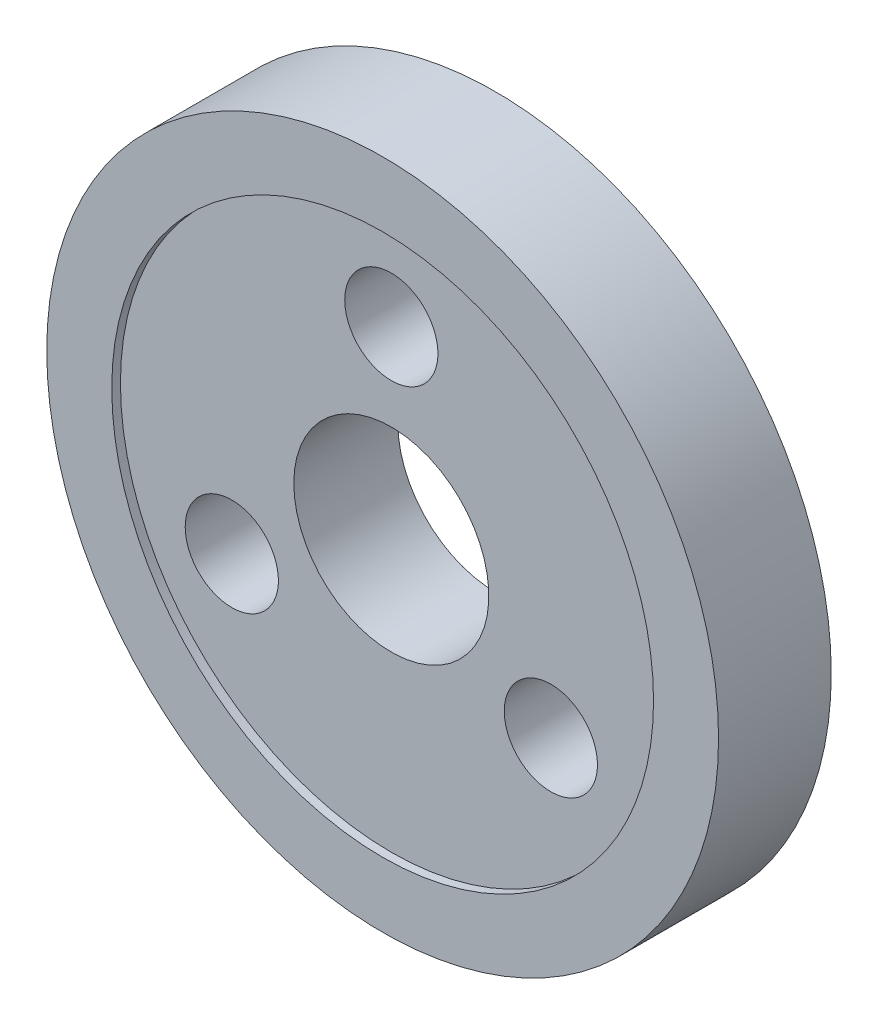
SolidWorks part; units mm, degrees
material "PE Low/Medium Density"
ref_plane "Front Plane" through (0, 0, 0) normal (0, 0, 1) x (1, 0, 0)
ref_plane "Top Plane" through (0, 0, 0) normal (0, 1, 0) x (1, 0, 0)
ref_plane "Right Plane" through (0, 0, 0) normal (1, 0, 0) x (0, 0, -1)
sketch "Sketch1" plane through (0, 0, 0) normal (0, 0, 1) x (1, 0, 0)
  circle A0 centre (0, 0) radius 12.5
  circle A1 centre (0, 0) radius 15.5
  dimension "D1" = 25
  dimension "D2" = 3
extrude "Boss-Extrude1" add sketch "Sketch1" along normal blind 0.4
sketch "Sketch2" plane through (0, 0, 0) normal (0, 0, -1) x (-1, 0, 0)
  circle A0 centre (0, 0) radius 15.5
  circle A1 centre (0, 0) radius 4.5
  circle A3 centre (0, 0) radius 15.5 construction
  dimension "D2" = 9
extrude "Boss-Extrude2" add sketch "Sketch2" along normal blind 4.8
hole_wizard "M4 Clearance Hole1" positions "Sketch4" profile "Sketch5" hole size "M4" standard "ANSI Metric" end condition through all
sketch "Sketch4" plane through (0, 0, -4.8) normal (0, 0, -1) x (-1, 0, 0)
  line L0 (-7.3612, -4.25) -> (0, 0) construction
  line L3 (0, 0) -> (7.3612, -4.25) construction
  line L6 (0, 8.5) -> (0, 4.5) construction
  line L7 (0, 8.5) -> (0, 12.5) construction
  circle A0 centre (0, 0) radius 4.5 construction
  circle A1 centre (0, 0) radius 8.5 construction
  circle A2 centre (0, 0) radius 4.5 construction
  circle A4 centre (0, 0) radius 12.5 construction
  point P0 (0, 8.5)
  point P2 (7.3612, -4.25)
  point P4 (-7.3612, -4.25)
  dimension "D1" = 25
  dimension "D2" = 120
  dimension "D3" = 120
sketch "Sketch5" plane through (0, 8.5, -4.8) normal (1, 0, 0) x (0, 1, 0)
  line L0 (0, 0) -> (0, 5.2)
  line L1 (0, 5.2) -> (2.15, 5.2)
  line L2 (2.15, 5.2) -> (2.15, 0)
  line L5 (2.15, 0) -> (0, 0)
  line L11 (0, -6.35) -> (0, 107.95) construction
  dimension "Thru Hole Dia." = 4.3
  dimension "Thru Hole Depth" = 5.2
